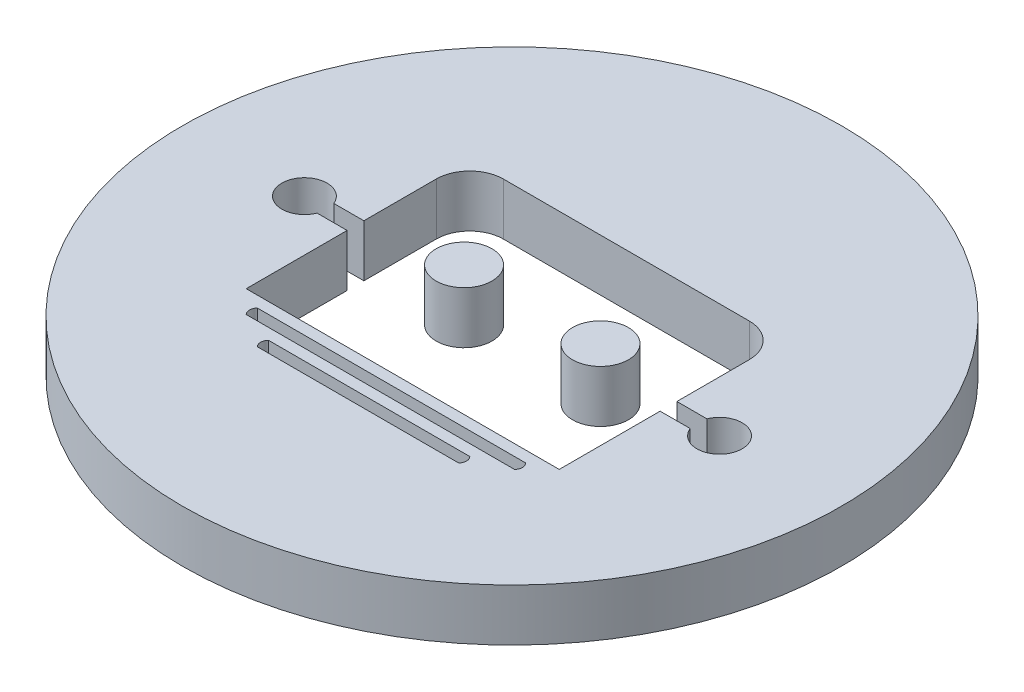
SolidWorks part; units mm, degrees
ref_plane "Front Plane" through (0, 0, 0) normal (0, 0, 1) x (1, 0, 0)
ref_plane "Top Plane" through (0, 0, 0) normal (0, 1, 0) x (1, 0, 0)
ref_plane "Right Plane" through (0, 0, 0) normal (1, 0, 0) x (0, 0, -1)
sketch "Sketch3" plane through (0, 0, 0) normal (0, 1, 0) x (1, 0, 0)
  line L0 (-35.6565, 106.4543) -> (-35.6565, 111.2038) construction
  line L1 (-55.1565, 106.4543) -> (-16.1565, 106.4543) construction
  line L2 (-55.1565, 106.4543) -> (-55.1565, 67.4543) construction
  line L3 (-55.1565, 67.4543) -> (-16.1565, 67.4543) construction
  line L4 (-16.1565, 106.4543) -> (-16.1565, 67.4543) construction
  circle A2 centre (-35.6565, 86.8647) radius 19
  circle A3 centre (-35.6565, 86.8647) radius 22
  line B0 (-44.6796, 80.5643) -> (-44.6796, 86.3813)
  line B1 (-42.746, 93.4543) -> (-28.567, 93.4543)
  line B2 (-26.6335, 91.5208) -> (-26.6335, 87.3481)
  line B3 (-26.6335, 87.3481) -> (-24.9009, 87.3481)
  line B4 (-24.9009, 86.3813) -> (-26.6335, 86.3813)
  line B5 (-26.6335, 86.3813) -> (-26.6335, 80.5643)
  line B6 (-26.6335, 80.5643) -> (-44.6796, 80.5643)
  line B7 (-46.4122, 87.3481) -> (-44.6796, 87.3481)
  line B8 (-44.6796, 86.3813) -> (-46.4122, 86.3813)
  line B9 (-43.3905, 79.9198) -> (-27.9225, 79.9198)
  line B10 (-43.3905, 79.2753) -> (-27.9225, 79.2753)
  line B11 (-41.457, 78.6308) -> (-29.856, 78.6308)
  line B12 (-41.457, 77.9863) -> (-29.856, 77.9863)
  line B13 (-44.6796, 87.3481) -> (-44.6796, 91.5208)
  line B14 (-35.6565, 86.8647) -> (-35.6565, 86.008) construction
  line B15 (-36.6157, 86.8647) -> (-34.909, 86.8647) construction
  circle B16 centre (-39.5884, 88.0327) radius 1.6113
  circle B17 centre (-31.7247, 88.0327) radius 1.6113
  arc B18 (-46.4122, 87.3481) -> (-46.4122, 86.3813) centre (-47.6224, 86.8647) ccw
  arc B19 (-24.9009, 86.3813) -> (-24.9009, 87.3481) centre (-23.6906, 86.8647) ccw
  arc B20 (-42.746, 93.4543) -> (-44.6796, 91.5208) centre (-42.746, 91.5208) ccw
  arc B21 (-26.6335, 91.5208) -> (-28.567, 93.4543) centre (-28.567, 91.5208) ccw
  arc B22 (-43.3905, 79.9198) -> (-43.3905, 79.2753) centre (-43.0683, 79.5975) ccw
  arc B23 (-41.457, 78.6308) -> (-41.457, 77.9863) centre (-41.1348, 78.3085) ccw
  arc B24 (-29.856, 78.6308) -> (-29.856, 77.9863) centre (-30.1783, 78.3085) cw
  arc B25 (-27.9225, 79.9198) -> (-27.9225, 79.2753) centre (-28.2447, 79.5975) cw
  dimension "D1" = 39
  dimension "D4" = 38
  dimension "D5" = 3
  dimension "D2" = 39
  dimension "D3" = 13
sketch_block_instance "Block3-1"
sketch_block "Block3"
extrude "Boss-Extrude1" add sketch "Sketch3" along normal blind 3 contours A2
sketch "Sketch6" plane through (0, 3, 0) normal (0, 1, 0) x (1, 0, 0)
  line L0 (-35.6565, 106.4543) -> (-35.6565, 116.1951) construction
  line L1 (-55.1565, 106.4543) -> (-16.1565, 106.4543) construction
  line L2 (-55.1565, 106.4543) -> (-55.1565, 67.4543) construction
  line L3 (-55.1565, 67.4543) -> (-16.1565, 67.4543) construction
  line L4 (-16.1565, 106.4543) -> (-16.1565, 67.4543) construction
  circle A0 centre (-35.6565, 86.8647) radius 19 construction
  circle A2 centre (-35.6565, 86.8647) radius 19.5 construction
  circle A3 centre (-35.6565, 86.8647) radius 22.5 construction
  line B0 (-44.6796, 80.5643) -> (-44.6796, 86.3813)
  line B1 (-42.746, 93.4543) -> (-28.567, 93.4543)
  line B2 (-26.6335, 91.5208) -> (-26.6335, 87.3481)
  line B3 (-26.6335, 87.3481) -> (-24.9009, 87.3481)
  line B4 (-24.9009, 86.3813) -> (-26.6335, 86.3813)
  line B5 (-26.6335, 86.3813) -> (-26.6335, 80.5643)
  line B6 (-26.6335, 80.5643) -> (-44.6796, 80.5643)
  line B7 (-46.4122, 87.3481) -> (-44.6796, 87.3481)
  line B8 (-44.6796, 86.3813) -> (-46.4122, 86.3813)
  line B9 (-43.3905, 79.9198) -> (-27.9225, 79.9198)
  line B10 (-43.3905, 79.2753) -> (-27.9225, 79.2753)
  line B11 (-41.457, 78.6308) -> (-29.856, 78.6308)
  line B12 (-41.457, 77.9863) -> (-29.856, 77.9863)
  line B13 (-44.6796, 87.3481) -> (-44.6796, 91.5208)
  line B14 (-35.6565, 86.8647) -> (-35.6565, 86.008) construction
  line B15 (-36.6157, 86.8647) -> (-34.909, 86.8647) construction
  circle B16 centre (-39.5884, 88.0327) radius 1.6113
  circle B17 centre (-31.7247, 88.0327) radius 1.6113
  arc B18 (-46.4122, 87.3481) -> (-46.4122, 86.3813) centre (-47.6224, 86.8647) ccw
  arc B19 (-24.9009, 86.3813) -> (-24.9009, 87.3481) centre (-23.6906, 86.8647) ccw
  arc B20 (-42.746, 93.4543) -> (-44.6796, 91.5208) centre (-42.746, 91.5208) ccw
  arc B21 (-26.6335, 91.5208) -> (-28.567, 93.4543) centre (-28.567, 91.5208) ccw
  arc B22 (-43.3905, 79.9198) -> (-43.3905, 79.2753) centre (-43.0683, 79.5975) ccw
  arc B23 (-41.457, 78.6308) -> (-41.457, 77.9863) centre (-41.1348, 78.3085) ccw
  arc B24 (-29.856, 78.6308) -> (-29.856, 77.9863) centre (-30.1783, 78.3085) cw
  arc B25 (-27.9225, 79.9198) -> (-27.9225, 79.2753) centre (-28.2447, 79.5975) cw
  dimension "D1" = 39
  dimension "D4" = 0
  dimension "D5" = 3
  dimension "D2" = 39
  dimension "D3" = 13
sketch_block_instance "Block3-4"
extrude "Cut-Extrude1" cut sketch "Sketch6" against normal through all
